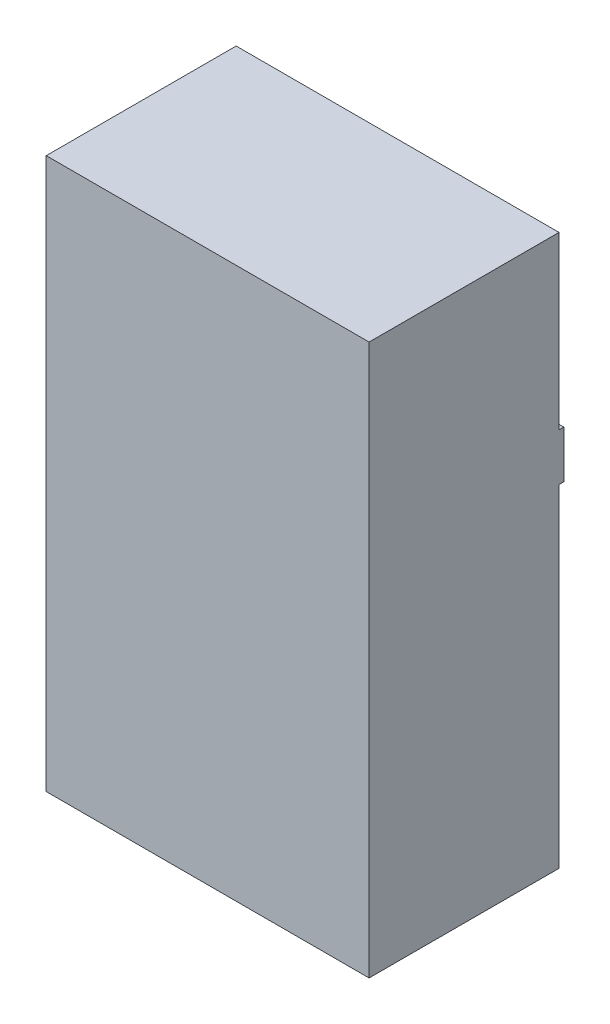
SolidWorks part; units mm, degrees
ref_plane "Front Plane" through (0, 0, 0) normal (0, 0, 1) x (1, 0, 0)
ref_plane "Top Plane" through (0, 0, 0) normal (0, 1, 0) x (1, 0, 0)
ref_plane "Right Plane" through (0, 0, 0) normal (1, 0, 0) x (0, 0, -1)
sketch "Sketch1" plane through (0, 0, 0) normal (0, 0, 1) x (1, 0, 0)
  line L1 (0, 0) -> (34, 0)
  line L2 (0, 0) -> (0, 58)
  line L3 (0, 58) -> (34, 58)
  line L4 (34, 0) -> (34, 58)
  dimension "D1" = 34
  dimension "D2" = 58
extrude "Boss-Extrude1" add sketch "Sketch1" along normal blind 20
sketch "Sketch2" plane through (0, 0, 0) normal (0, -1, 0) x (1, 0, 0)
  text T0 "120V"
extrude "Cut-Extrude1" cut sketch "Sketch2" against normal blind 5
sketch "Sketch3" plane through (0, 0, 0) normal (0, 0, -1) x (-1, 0, 0)
  line L0 (-34, 0) -> (-34, 58) construction
  line L1 (-34, 40) -> (0, 40)
  line L2 (-34, 40) -> (-34, 35)
  line L3 (-34, 35) -> (0, 35)
  line L4 (0, 40) -> (0, 35)
  line L5 (0, 58) -> (0, 0) construction
  line L6 (0, 0) -> (-34, 0) construction
  dimension "D1" = 5
  dimension "D2" = 35
extrude "Boss-Extrude2" add sketch "Sketch3" along normal blind 0.5
